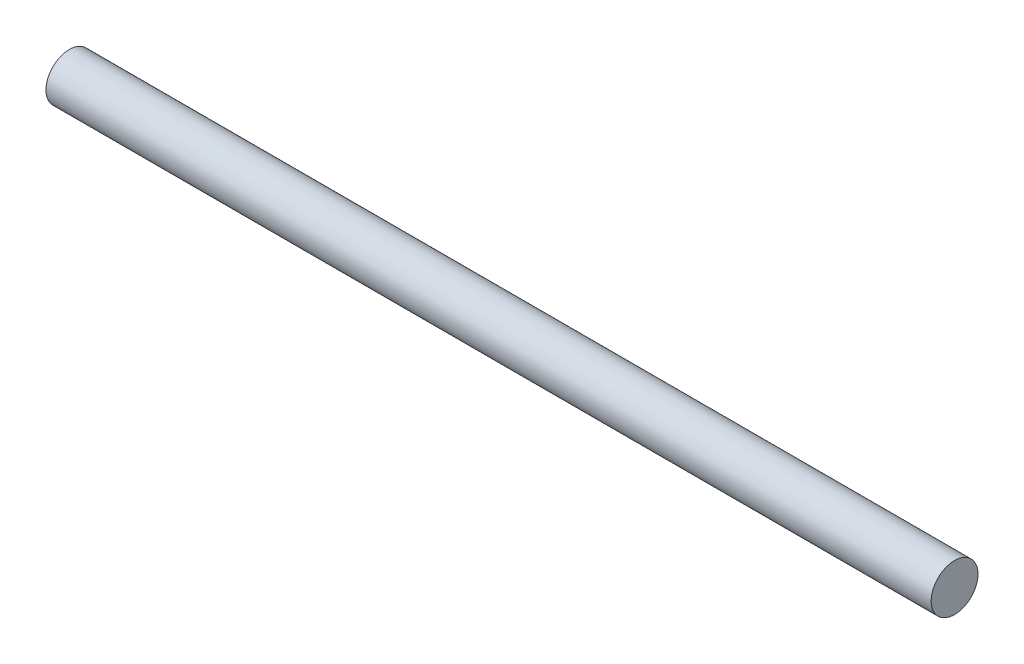
SolidWorks part; units mm, degrees
material "AISI 1020"
ref_plane "Plano frontal" through (0, 0, 0) normal (0, 0, 1) x (1, 0, 0)
ref_plane "Plano superior" through (0, 0, 0) normal (0, 1, 0) x (1, 0, 0)
ref_plane "Plano direito" through (0, 0, 0) normal (1, 0, 0) x (0, 0, -1)
sketch "Esboço1" plane through (0, 0, 0) normal (1, 0, 0) x (0, 0, -1)
  circle A0 centre (0, 0) radius 3.9688
extrude "Ressalto-extrusão1" add sketch "Esboço1" along normal blind 150
